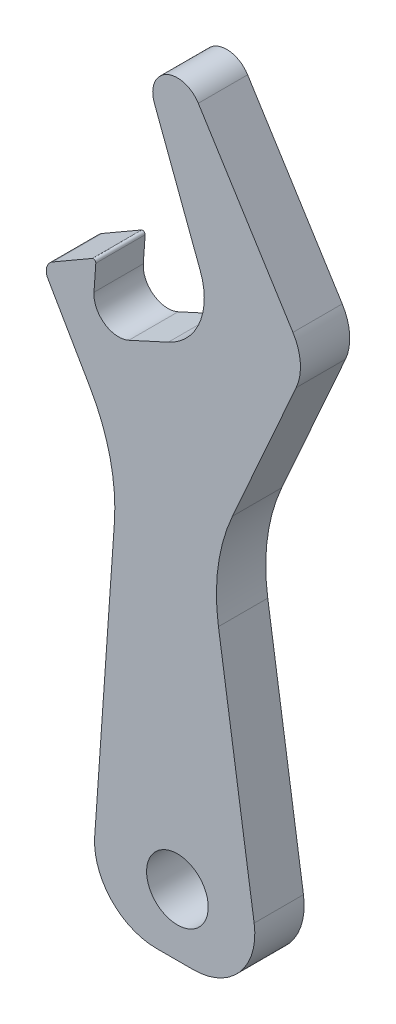
SolidWorks part; units mm, degrees
material "Nichtrostender Chromstahl"
ref_plane "Vorne" through (0, 0, 0) normal (0, 0, 1) x (1, 0, 0)
ref_plane "Oben" through (0, 0, 0) normal (0, 1, 0) x (1, 0, 0)
ref_plane "Rechts" through (0, 0, 0) normal (1, 0, 0) x (0, 0, -1)
sketch "Skizze1" plane through (0, 0, 0) normal (0, 0, 1) x (1, 0, 0)
  line L0 (-1.7205, -5) -> (1.2795, -5)
  line L1 (6.2246, 0.739) -> (3.3285, 20.1171)
  line L2 (4.4606, 28.4353) -> (9.634, 40.0548)
  line L3 (9.37, 43.8046) -> (1.6951, 56.0614)
  line L4 (-1.8722, 54.2965) -> (1.8591, 44.3667)
  line L5 (-0.7425, 38.0606) -> (-3.9385, 36.5995)
  line L6 (-6.7652, 38.558) -> (-6.6175, 40.6702)
  line L7 (-6.917, 40.8573) -> (-10.134, 39)
  line L8 (-10.5, 37.634) -> (-7.0853, 31.7196)
  line L9 (-5.1122, 23.1732) -> (-6.7083, 0.3488)
  line L10 (0, -9.0513) -> (0, 61.195) construction
  line L11 (10.5, 42) -> (27.3385, 42) construction
  line L12 (-7, 35.2) -> (-7, 27.8826) construction
  line L13 (-6.7205, 0) -> (-6.7205, -5.8381) construction
  line L14 (6.2795, 0) -> (6.2795, -8.1444) construction
  line L15 (-11, 38.5) -> (-18.7671, 38.5) construction
  arc A0 (1.6951, 56.0614) -> (-1.8722, 54.2965) centre (0, 55) ccw
  arc A1 (-1.7205, -5) -> (-6.7083, 0.3488) centre (-1.7205, 0) cw
  arc A2 (1.2795, -5) -> (6.2246, 0.739) centre (1.2795, 0) ccw
  arc A3 (3.3285, 20.1171) -> (4.4606, 28.4353) centre (18.1638, 22.3342) cw
  arc A4 (-7.0853, 31.7196) -> (-5.1122, 23.1732) centre (-20.0757, 24.2196) cw
  arc A5 (1.8591, 44.3667) -> (-0.7425, 38.0606) centre (-2.8213, 42.6079) cw
  arc A6 (-3.9385, 36.5995) -> (-6.7652, 38.558) centre (-4.7701, 38.4185) cw
  arc A7 (-10.134, 39) -> (-10.5, 37.634) centre (-9.634, 38.134) ccw
  arc A8 (-6.917, 40.8573) -> (-6.6175, 40.6702) centre (-6.817, 40.6841) cw
  circle A9 centre (0, 0) radius 2.5
  arc A10 (9.634, 40.0548) -> (9.37, 43.8046) centre (5.9798, 41.6818) ccw
  point P17 (-7.0823, -5)
  point P20 (7.0823, -5)
  point P34 (3.5, 40)
  dimension "D2" = 5
  dimension "D3" = 13
  dimension "D4" = 2
  dimension "D14" = 15
  dimension "D21" = 5
  dimension "D22" = 2
  dimension "D23" = 1
  dimension "D24" = 0.2
  dimension "D25" = 5
  dimension "D26" = 4
  dimension "D1" = 5
  dimension "D5" = 45
  dimension "D6" = 47
  dimension "D7" = 3.5
  dimension "D8" = 40.2
  dimension "D9" = 43.5
  dimension "D10" = 60
  dimension "D11" = 11
  dimension "D12" = 10.5
  dimension "D13" = 66
  dimension "D15" = 7
  dimension "D16" = 4
  dimension "D17" = 4
  dimension "D18" = 8.5
  dimension "D19" = 30
  dimension "D20" = 60
extrude "Linear austragen1" add sketch "Skizze1" along normal blind 4
